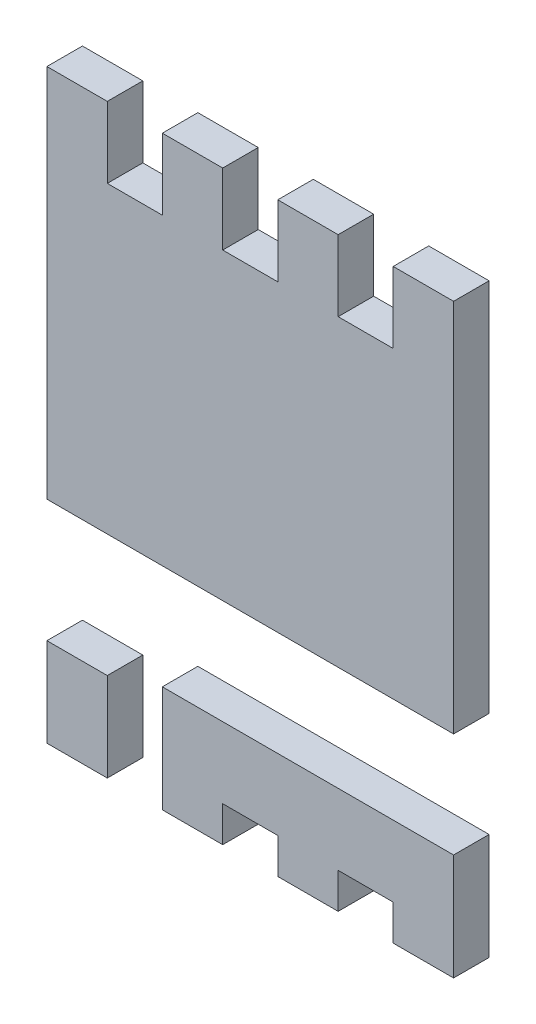
SolidWorks part; units mm, degrees
ref_plane "Спереди" through (0, 0, 0) normal (0, 0, 1) x (1, 0, 0)
ref_plane "Сверху" through (0, 0, 0) normal (0, 1, 0) x (1, 0, 0)
ref_plane "Справа" through (0, 0, 0) normal (1, 0, 0) x (0, 0, -1)
sketch "Эскиз2" plane through (0, 0, 0) normal (0, 0, 1) x (1, 0, 0)
  line L0 (-1.145, 1.65) -> (-1.145, -0.46)
  line L1 (-1.145, -0.46) -> (1.145, -0.46)
  line L2 (1.145, -0.46) -> (1.145, 1.65)
  line L3 (1.145, 1.65) -> (0.805, 1.65)
  line L4 (0.805, 1.65) -> (0.805, 1.25)
  line L5 (0.805, 1.25) -> (0.495, 1.25)
  line L6 (0.495, 1.25) -> (0.495, 1.65)
  line L7 (-0.495, 1.65) -> (-0.495, 1.25)
  line L8 (-0.495, 1.25) -> (-0.805, 1.25)
  line L9 (-0.805, 1.25) -> (-0.805, 1.65)
  line L10 (-0.805, 1.65) -> (-1.145, 1.65)
  line L11 (-0.495, 1.65) -> (-0.155, 1.65)
  line L12 (-0.155, 1.65) -> (-0.155, 1.25)
  line L13 (-0.155, 1.25) -> (0.155, 1.25)
  line L14 (0.155, 1.25) -> (0.155, 1.65)
  line L15 (0.155, 1.65) -> (0.495, 1.65)
  line L16 (1.145, -1.65) -> (1.145, -1.05)
  line L17 (1.145, -1.05) -> (-0.495, -1.05)
  line L18 (-0.495, -1.05) -> (-0.495, -1.65)
  line L19 (-0.495, -1.65) -> (-0.155, -1.65)
  line L20 (-0.155, -1.65) -> (-0.155, -1.45)
  line L21 (-0.155, -1.45) -> (0.155, -1.45)
  line L22 (0.155, -1.45) -> (0.155, -1.65)
  line L23 (0.155, -1.65) -> (0.495, -1.65)
  line L24 (0.495, -1.65) -> (0.495, -1.45)
  line L25 (0.495, -1.45) -> (0.805, -1.45)
  line L26 (0.805, -1.45) -> (0.805, -1.65)
  line L27 (0.805, -1.65) -> (1.145, -1.65)
  line L28 (-0.805, -1.65) -> (-0.805, -1.15)
  line L29 (-0.805, -1.15) -> (-1.145, -1.15)
  line L30 (-1.145, -1.15) -> (-1.145, -1.65)
  line L31 (-1.145, -1.65) -> (-0.805, -1.65)
  dimension "D1" = 2.29
  dimension "D2" = 1.71
  dimension "D3" = 0.31
  dimension "D4" = 0.31
  dimension "D5" = 0.31
  dimension "D6" = 0.6
  dimension "D7" = 0.5
  dimension "D8" = 1.145
  dimension "D9" = 0.34
  dimension "D10" = 0.4
  dimension "D11" = 3.3
  dimension "D12" = 0.46
  dimension "D13" = 0.2
extrude "Бобышка-Вытянуть1" add sketch "Эскиз2" along normal blind 0.2
